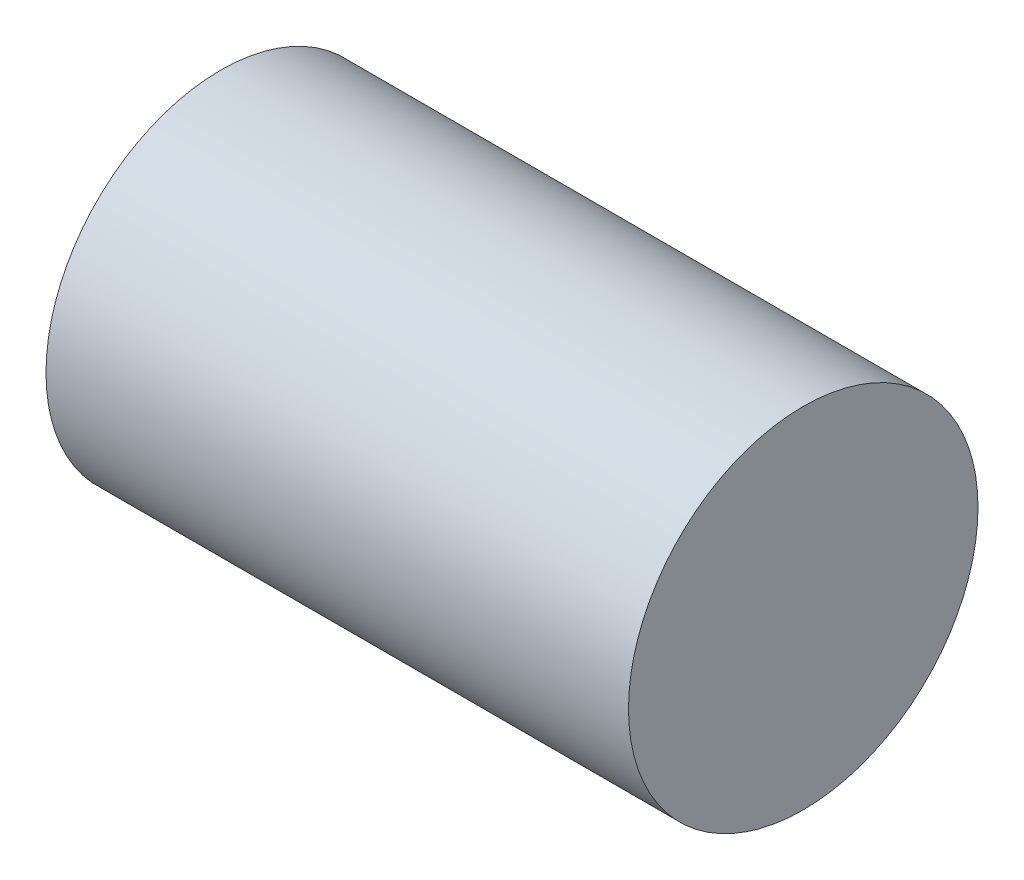
SolidWorks part; units mm, degrees
material "1023 al carbonio, lamiera (SS)"
ref_plane "Piano frontale" through (0, 0, 0) normal (0, 0, 1) x (1, 0, 0)
ref_plane "Piano superiore" through (0, 0, 0) normal (0, 1, 0) x (1, 0, 0)
ref_plane "Piano destro" through (0, 0, 0) normal (1, 0, 0) x (0, 0, -1)
sketch "Schizzo1" plane through (0, 0, 0) normal (0, 0, 1) x (1, 0, 0)
  line L1 (0, 0) -> (40, 0)
  line L2 (0, 0) -> (0, 12)
  line L3 (0, 12) -> (40, 12)
  line L4 (40, 0) -> (40, 12)
  dimension "D1" = 12
  dimension "D2" = 40
revolve "Rivoluzione1" add sketch "Schizzo1" angle 360 about L3
